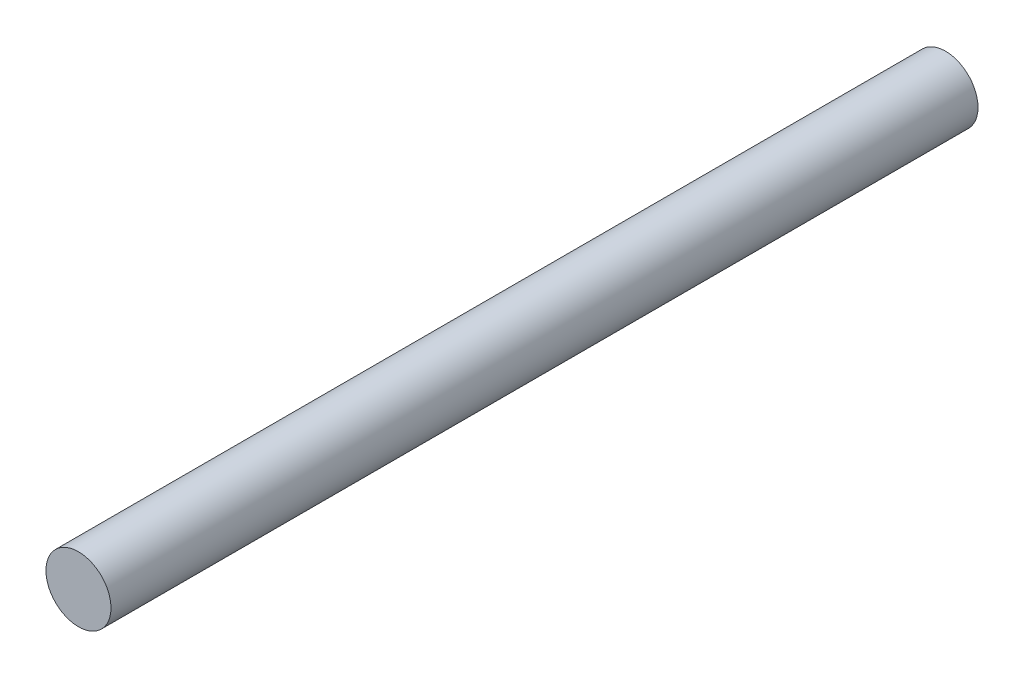
SolidWorks part; units mm, degrees
ref_plane "前基準面" through (0, 0, 0) normal (0, 0, 1) x (1, 0, 0)
ref_plane "上基準面" through (0, 0, 0) normal (0, 1, 0) x (1, 0, 0)
ref_plane "右基準面" through (0, 0, 0) normal (1, 0, 0) x (0, 0, -1)
sketch "草圖1" plane through (0, 0, 0) normal (0, 0, 1) x (1, 0, 0)
  circle A0 centre (0, 0) radius 1.5
  dimension "D1" = 3
extrude "填料-伸長1" add sketch "草圖1" along normal blind 40
